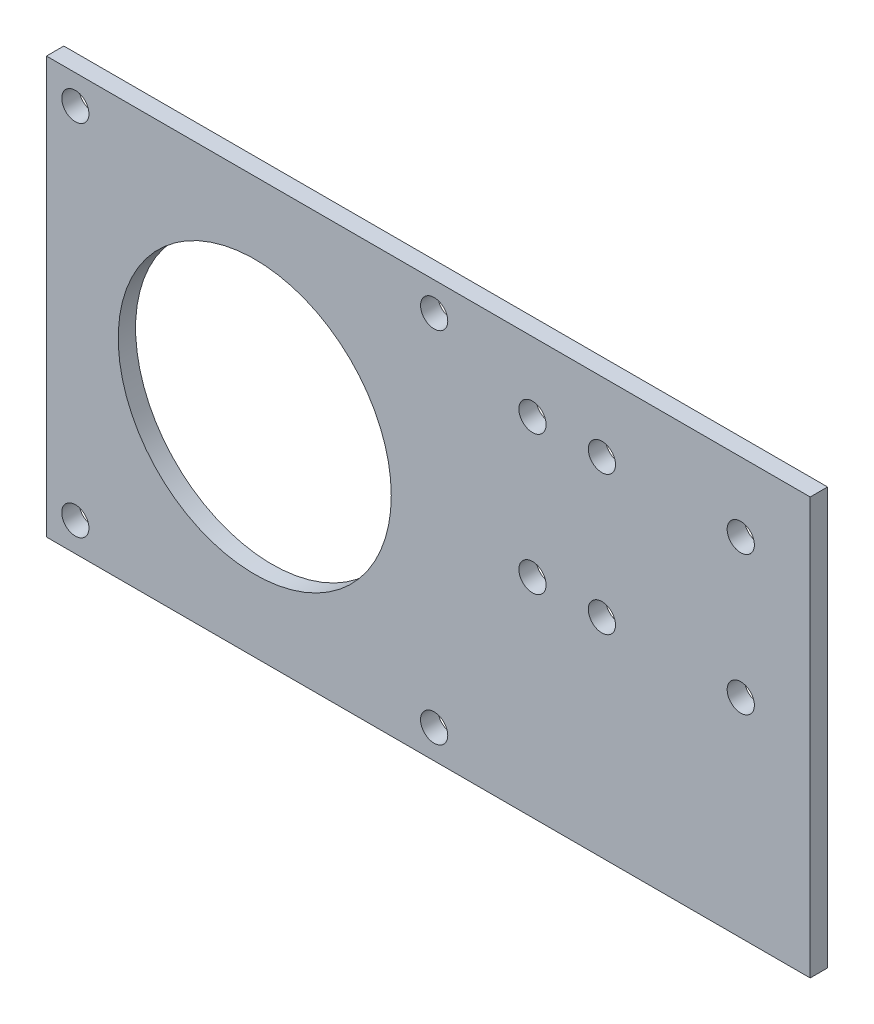
SolidWorks part; units mm, degrees
ref_plane "Front Plane" through (0, 0, 0) normal (0, 0, 1) x (1, 0, 0)
ref_plane "Top Plane" through (0, 0, 0) normal (0, 1, 0) x (1, 0, 0)
ref_plane "Right Plane" through (0, 0, 0) normal (1, 0, 0) x (0, 0, -1)
sketch "Sketch1" plane through (0, 0, 0) normal (0, 0, 1) x (1, 0, 0)
  line L0 (25.4, -189.5818) -> (25.4, 189.5818) construction
  line L1 (-114.3, 189.5818) -> (25.4, 189.5818)
  line L2 (-114.3, 189.5818) -> (-114.3, 113.3818)
  line L3 (-114.3, 113.3818) -> (25.4, 113.3818)
  line L4 (25.4, 189.5818) -> (25.4, 113.3818)
  circle A0 centre (-109.0168, 118.665) radius 2.4892 construction
  circle A1 centre (-76.2, 151.4818) radius 24.972 construction
  circle A2 centre (-43.3832, 184.2986) radius 2.4892 construction
  circle A3 centre (-25.4, 151.4818) radius 2.4892 construction
  circle A4 centre (-25.4, 176.8818) radius 2.4892 construction
  circle A5 centre (-12.7, 151.4818) radius 2.4892 construction
  circle A6 centre (-12.7, 176.8818) radius 2.4892 construction
  circle A7 centre (12.7, 151.4818) radius 2.4892 construction
  circle A8 centre (12.7, 176.8818) radius 2.4892 construction
  circle A9 centre (-109.0168, 118.665) radius 2.4892
  circle A10 centre (-76.2, 151.4818) radius 24.972
  circle A11 centre (-43.3832, 184.2986) radius 2.4892
  circle A12 centre (-25.4, 151.4818) radius 2.4892
  circle A13 centre (-25.4, 176.8818) radius 2.4892
  circle A14 centre (-12.7, 151.4818) radius 2.4892
  circle A15 centre (-12.7, 176.8818) radius 2.4892
  circle A16 centre (12.7, 151.4818) radius 2.4892
  circle A17 centre (12.7, 176.8818) radius 2.4892
  circle A18 centre (-109.0168, 184.2986) radius 2.4892 construction
  circle A19 centre (-43.3832, 118.665) radius 2.4892 construction
  circle A20 centre (-109.0168, 184.2986) radius 2.4892
  circle A21 centre (-43.3832, 118.665) radius 2.4892
  dimension "D1" = 76.2
extrude "Boss-Extrude1" add sketch "Sketch1" along normal blind 3.175
equation "\"Thick\"= \"in\""
